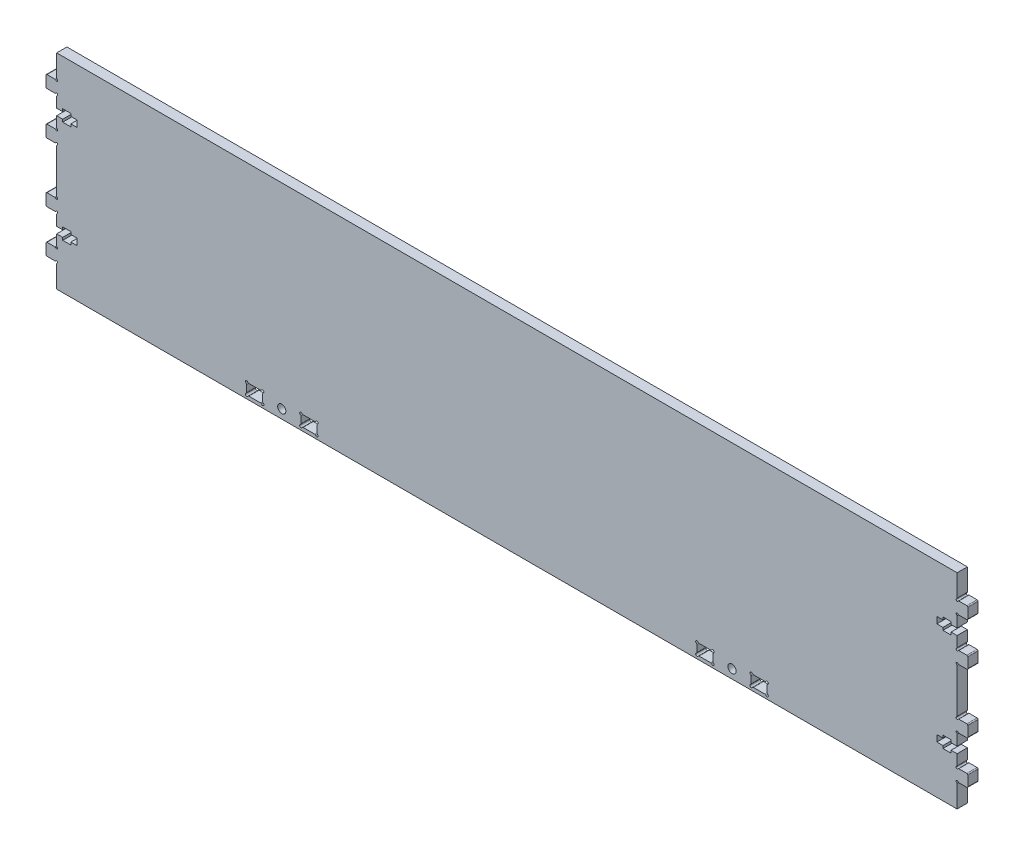
SolidWorks part; units mm, degrees
ref_plane "Alzado" through (0, 0, 0) normal (0, 0, 1) x (1, 0, 0)
ref_plane "Planta" through (0, 0, 0) normal (0, 1, 0) x (1, 0, 0)
ref_plane "Vista lateral" through (0, 0, 0) normal (1, 0, 0) x (0, 0, -1)
sketch "Croquis1" plane through (0, 0, 0) normal (0, 0, 1) x (1, 0, 0)
  line L0 (-176, 0) -> (-196, 0) construction
  line L2 (-175.9989, 28.5513) -> (-175.9989, 11.4487)
  line L3 (-175.9989, -20) -> (176.0011, -20)
  line L4 (-176.6843, -10.7633) -> (-179.7689, -10.7633)
  line L7 (176.0011, 1.2663) -> (176.0011, -1.2663) construction
  line L12 (-175.9989, -11.4487) -> (-175.9989, -20)
  line L27 (-168.0847, 0) -> (168.0869, 0) construction
  line L36 (-175.9989, -18.5) -> (176.0011, -18.5) construction
  line L46 (-175.9989, -14.5) -> (176.0011, -14.5) construction
  line L47 (-180.1646, -10.3676) -> (-180.1646, -6.4105)
  line L48 (-179.7689, -6.0148) -> (-176.6843, -6.0148)
  line L49 (-175.9989, -1.2663) -> (-173.6247, -1.2663)
  line L50 (-173.6247, -1.2663) -> (-173.6247, -2.2753)
  line L51 (-173.6247, -2.2753) -> (-170.459, -2.2753)
  line L52 (-170.459, -2.2753) -> (-170.459, -1.2663)
  line L53 (-170.459, -1.2663) -> (-168.0847, -1.2663)
  line L54 (-168.0847, -1.2663) -> (-168.0847, 1.2663)
  line L55 (-168.0847, 1.2663) -> (-170.459, 1.2663)
  line L56 (-170.459, 1.2663) -> (-170.459, 2.2753)
  line L57 (-170.459, 2.2753) -> (-173.6247, 2.2753)
  line L58 (-173.6247, 2.2753) -> (-173.6247, 1.2663)
  line L59 (-173.6247, 1.2663) -> (-175.9989, 1.2663)
  line L60 (-175.9989, 1.2663) -> (-175.9989, 5.3294)
  line L61 (-176.6843, 6.0148) -> (-179.7689, 6.0148)
  line L62 (-180.1646, 6.4105) -> (-180.1646, 10.3676)
  line L63 (-179.7689, 10.7633) -> (-176.6843, 10.7633)
  line L64 (-175.9989, -1.2663) -> (-175.9989, -5.3294)
  line L65 (176.0011, -11.4487) -> (176.0011, -20)
  line L66 (176.0011, -1.2663) -> (176.0011, -5.3294)
  line L67 (179.7711, 10.7633) -> (176.6865, 10.7633)
  line L68 (180.1668, 6.4105) -> (180.1668, 10.3676)
  line L69 (176.6865, 6.0148) -> (179.7711, 6.0148)
  line L70 (176.0011, 1.2663) -> (176.0011, 5.3294)
  line L71 (173.6269, 1.2663) -> (176.0011, 1.2663)
  line L72 (173.6269, 2.2753) -> (173.6269, 1.2663)
  line L73 (170.4612, 2.2753) -> (173.6269, 2.2753)
  line L74 (170.4612, 1.2663) -> (170.4612, 2.2753)
  line L75 (168.0869, 1.2663) -> (170.4612, 1.2663)
  line L76 (168.0869, -1.2663) -> (168.0869, 1.2663)
  line L77 (170.4612, -1.2663) -> (168.0869, -1.2663)
  line L78 (170.4612, -2.2753) -> (170.4612, -1.2663)
  line L79 (173.6269, -2.2753) -> (170.4612, -2.2753)
  line L80 (173.6269, -1.2663) -> (173.6269, -2.2753)
  line L81 (176.0011, -1.2663) -> (173.6269, -1.2663)
  line L82 (179.7711, -6.0148) -> (176.6865, -6.0148)
  line L83 (180.1668, -10.3676) -> (180.1668, -6.4105)
  line L84 (176.6865, -10.7633) -> (179.7711, -10.7633)
  line L85 (96.3671, -14.35) -> (100.8351, -14.35)
  line L86 (88.0011, -34.8253) -> (88.0011, -20) construction
  line L131 (176.0011, 28.5513) -> (176.0011, 11.4487)
  line L136 (101.7011, -15.2161) -> (101.7011, -17.7839)
  line L138 (-87.9989, -34.8253) -> (-87.9989, -20) construction
  line L139 (100.8351, -18.65) -> (96.3671, -18.65)
  line L140 (95.5011, -17.7839) -> (95.5011, -15.2161)
  line L141 (75.1671, -14.35) -> (79.6351, -14.35)
  line L142 (80.5011, -15.2161) -> (80.5011, -17.7839)
  line L143 (79.6351, -18.65) -> (75.1671, -18.65)
  line L144 (74.3011, -17.7839) -> (74.3011, -15.2161)
  line L145 (-87.9989, -18.5) -> (-87.9989, -14.5) construction
  line L146 (-101.6989, -17.7839) -> (-101.6989, -15.2161)
  line L147 (-74.2989, -15.2161) -> (-74.2989, -17.7839)
  line L148 (-95.4989, -15.2161) -> (-95.4989, -17.7839)
  line L149 (-96.3649, -18.65) -> (-100.8329, -18.65)
  line L150 (-100.8329, -14.35) -> (-96.3649, -14.35)
  line L151 (-79.6329, -14.35) -> (-75.1649, -14.35)
  line L152 (-80.4989, -17.7839) -> (-80.4989, -15.2161)
  line L153 (-75.1649, -18.65) -> (-79.6329, -18.65)
  line L154 (88.0011, -18.5) -> (88.0011, -14.5) construction
  line L161 (-168.0847, 40) -> (168.0869, 40) construction
  line L162 (176.0011, 38.7337) -> (176.0011, 41.2663) construction
  line L163 (-176, 40) -> (-196, 40) construction
  line L180 (176.6865, 50.7633) -> (179.7711, 50.7633)
  line L181 (180.1668, 50.3676) -> (180.1668, 46.4105)
  line L182 (179.7711, 46.0148) -> (176.6865, 46.0148)
  line L183 (176.0011, 41.2663) -> (173.6269, 41.2663)
  line L184 (173.6269, 41.2663) -> (173.6269, 42.2753)
  line L185 (173.6269, 42.2753) -> (170.4612, 42.2753)
  line L186 (170.4612, 42.2753) -> (170.4612, 41.2663)
  line L187 (170.4612, 41.2663) -> (168.0869, 41.2663)
  line L188 (168.0869, 41.2663) -> (168.0869, 38.7337)
  line L189 (168.0869, 38.7337) -> (170.4612, 38.7337)
  line L190 (170.4612, 38.7337) -> (170.4612, 37.7247)
  line L191 (170.4612, 37.7247) -> (173.6269, 37.7247)
  line L192 (173.6269, 37.7247) -> (173.6269, 38.7337)
  line L193 (173.6269, 38.7337) -> (176.0011, 38.7337)
  line L194 (176.0011, 38.7337) -> (176.0011, 34.6706)
  line L195 (176.6865, 33.9852) -> (179.7711, 33.9852)
  line L196 (180.1668, 33.5895) -> (180.1668, 29.6324)
  line L197 (179.7711, 29.2367) -> (176.6865, 29.2367)
  line L198 (176.0011, 41.2663) -> (176.0011, 45.3294)
  line L199 (176.0011, 51.4487) -> (176.0011, 60)
  line L200 (-175.9989, 41.2663) -> (-175.9989, 45.3294)
  line L201 (-179.7689, 29.2367) -> (-176.6843, 29.2367)
  line L202 (-180.1646, 33.5895) -> (-180.1646, 29.6324)
  line L203 (-176.6843, 33.9852) -> (-179.7689, 33.9852)
  line L204 (-175.9989, 38.7337) -> (-175.9989, 34.6706)
  line L205 (-173.6247, 38.7337) -> (-175.9989, 38.7337)
  line L206 (-173.6247, 37.7247) -> (-173.6247, 38.7337)
  line L207 (-170.459, 37.7247) -> (-173.6247, 37.7247)
  line L208 (-170.459, 38.7337) -> (-170.459, 37.7247)
  line L209 (-168.0847, 38.7337) -> (-170.459, 38.7337)
  line L210 (-168.0847, 41.2663) -> (-168.0847, 38.7337)
  line L211 (-170.459, 41.2663) -> (-168.0847, 41.2663)
  line L212 (-170.459, 42.2753) -> (-170.459, 41.2663)
  line L213 (-173.6247, 42.2753) -> (-170.459, 42.2753)
  line L214 (-173.6247, 41.2663) -> (-173.6247, 42.2753)
  line L215 (-175.9989, 41.2663) -> (-173.6247, 41.2663)
  line L216 (-179.7689, 46.0148) -> (-176.6843, 46.0148)
  line L217 (-180.1646, 50.3676) -> (-180.1646, 46.4105)
  line L218 (-175.9989, 51.4487) -> (-175.9989, 60)
  line L219 (-176.6843, 50.7633) -> (-179.7689, 50.7633)
  line L220 (-175.9989, 60) -> (176.0011, 60)
  arc A32 (-175.801, -11.106) -> (-175.9989, -11.4487) centre (-175.6032, -11.4487) ccw
  arc A33 (-175.801, -11.106) -> (-176.3416, -10.5654) centre (-175.9989, -10.7633) ccw
  arc A34 (-176.6843, -10.7633) -> (-176.3416, -10.5654) centre (-176.6843, -10.3676) ccw
  arc A35 (-180.1646, -10.3676) -> (-179.7689, -10.7633) centre (-179.7689, -10.3676) ccw
  arc A36 (-179.7689, -6.0148) -> (-180.1646, -6.4105) centre (-179.7689, -6.4105) ccw
  arc A37 (-176.3416, -6.2126) -> (-176.6843, -6.0148) centre (-176.6843, -6.4105) ccw
  arc A38 (-176.3416, -6.2126) -> (-175.801, -5.6721) centre (-175.9989, -6.0148) ccw
  arc A39 (-175.9989, -5.3294) -> (-175.801, -5.6721) centre (-175.6032, -5.3294) ccw
  arc A40 (-175.801, 5.6721) -> (-175.9989, 5.3294) centre (-175.6032, 5.3294) ccw
  arc A41 (-175.801, 5.6721) -> (-176.3416, 6.2126) centre (-175.9989, 6.0148) ccw
  arc A42 (-176.6843, 6.0148) -> (-176.3416, 6.2126) centre (-176.6843, 6.4105) ccw
  arc A43 (-180.1646, 6.4105) -> (-179.7689, 6.0148) centre (-179.7689, 6.4105) ccw
  arc A44 (-179.7689, 10.7633) -> (-180.1646, 10.3676) centre (-179.7689, 10.3676) ccw
  arc A45 (-176.3416, 10.5654) -> (-176.6843, 10.7633) centre (-176.6843, 10.3676) ccw
  arc A46 (-176.3416, 10.5654) -> (-175.801, 11.106) centre (-175.9989, 10.7633) ccw
  arc A47 (-175.9989, 11.4487) -> (-175.801, 11.106) centre (-175.6032, 11.4487) ccw
  arc A48 (176.0011, 11.4487) -> (175.8033, 11.106) centre (175.6054, 11.4487) cw
  arc A49 (176.3438, 10.5654) -> (175.8033, 11.106) centre (176.0011, 10.7633) cw
  arc A50 (176.3438, 10.5654) -> (176.6865, 10.7633) centre (176.6865, 10.3676) cw
  arc A51 (179.7711, 10.7633) -> (180.1668, 10.3676) centre (179.7711, 10.3676) cw
  arc A52 (180.1668, 6.4105) -> (179.7711, 6.0148) centre (179.7711, 6.4105) cw
  arc A53 (176.6865, 6.0148) -> (176.3438, 6.2126) centre (176.6865, 6.4105) cw
  arc A54 (175.8033, 5.6721) -> (176.3438, 6.2126) centre (176.0011, 6.0148) cw
  arc A55 (175.8033, 5.6721) -> (176.0011, 5.3294) centre (175.6054, 5.3294) cw
  arc A56 (176.0011, -5.3294) -> (175.8033, -5.6721) centre (175.6054, -5.3294) cw
  arc A57 (176.3438, -6.2126) -> (175.8033, -5.6721) centre (176.0011, -6.0148) cw
  arc A58 (176.3438, -6.2126) -> (176.6865, -6.0148) centre (176.6865, -6.4105) cw
  arc A59 (179.7711, -6.0148) -> (180.1668, -6.4105) centre (179.7711, -6.4105) cw
  arc A60 (180.1668, -10.3676) -> (179.7711, -10.7633) centre (179.7711, -10.3676) cw
  arc A61 (176.6865, -10.7633) -> (176.3438, -10.5654) centre (176.6865, -10.3676) cw
  arc A62 (175.8033, -11.106) -> (176.3438, -10.5654) centre (176.0011, -10.7633) cw
  arc A63 (175.8033, -11.106) -> (176.0011, -11.4487) centre (175.6054, -11.4487) cw
  arc A96 (95.5011, -15.2161) -> (95.2511, -14.7831) centre (95.0011, -15.2161) ccw
  arc A97 (95.9341, -14.1) -> (95.2511, -14.7831) centre (95.5011, -14.35) ccw
  arc A98 (95.9341, -14.1) -> (96.3671, -14.35) centre (96.3671, -13.85) ccw
  arc A99 (100.8351, -14.35) -> (101.2681, -14.1) centre (100.8351, -13.85) ccw
  arc A100 (101.9511, -14.783) -> (101.2681, -14.1) centre (101.7011, -14.35) ccw
  arc A101 (101.9511, -14.783) -> (101.7011, -15.2161) centre (102.2011, -15.2161) ccw
  arc A102 (101.7011, -17.7839) -> (101.9511, -18.2169) centre (102.2011, -17.7839) ccw
  arc A103 (101.2681, -18.9) -> (101.9511, -18.2169) centre (101.7011, -18.65) ccw
  arc A104 (101.2681, -18.9) -> (100.8351, -18.65) centre (100.8351, -19.15) ccw
  arc A105 (96.3671, -18.65) -> (95.9341, -18.9) centre (96.3671, -19.15) ccw
  arc A106 (95.2511, -18.2169) -> (95.9341, -18.9) centre (95.5011, -18.65) ccw
  arc A107 (95.2511, -18.2169) -> (95.5011, -17.7839) centre (95.0011, -17.7839) ccw
  arc A108 (74.3011, -15.2161) -> (74.0511, -14.7831) centre (73.8011, -15.2161) ccw
  arc A109 (74.7341, -14.1) -> (74.0511, -14.7831) centre (74.3011, -14.35) ccw
  arc A110 (74.7341, -14.1) -> (75.1671, -14.35) centre (75.1671, -13.85) ccw
  arc A111 (79.6351, -14.35) -> (80.0681, -14.1) centre (79.6351, -13.85) ccw
  arc A112 (80.7511, -14.783) -> (80.0681, -14.1) centre (80.5011, -14.35) ccw
  arc A113 (80.7511, -14.783) -> (80.5011, -15.2161) centre (81.0011, -15.2161) ccw
  arc A114 (80.5011, -17.7839) -> (80.7511, -18.2169) centre (81.0011, -17.7839) ccw
  arc A115 (80.0681, -18.9) -> (80.7511, -18.2169) centre (80.5011, -18.65) ccw
  arc A116 (80.0681, -18.9) -> (79.6351, -18.65) centre (79.6351, -19.15) ccw
  arc A117 (75.1671, -18.65) -> (74.7341, -18.9) centre (75.1671, -19.15) ccw
  arc A118 (74.0511, -18.217) -> (74.7341, -18.9) centre (74.3011, -18.65) ccw
  arc A119 (74.0511, -18.217) -> (74.3011, -17.7839) centre (73.8011, -17.7839) ccw
  circle A120 centre (88.0011, -16.5) radius 1.6
  arc A121 (-101.6989, -15.2161) -> (-101.9489, -14.7831) centre (-102.1989, -15.2161) ccw
  arc A122 (-79.6329, -18.65) -> (-80.0659, -18.9) centre (-79.6329, -19.15) ccw
  arc A123 (-74.0489, -14.783) -> (-74.2989, -15.2161) centre (-73.7989, -15.2161) ccw
  arc A124 (-96.3649, -14.35) -> (-95.9319, -14.1) centre (-96.3649, -13.85) ccw
  arc A125 (-95.2489, -14.783) -> (-95.9319, -14.1) centre (-95.4989, -14.35) ccw
  arc A126 (-95.9319, -18.9) -> (-95.2489, -18.2169) centre (-95.4989, -18.65) ccw
  arc A127 (-80.7489, -18.2169) -> (-80.4989, -17.7839) centre (-80.9989, -17.7839) ccw
  circle A128 centre (-87.9989, -16.5) radius 1.6
  arc A129 (-74.2989, -17.7839) -> (-74.0489, -18.2169) centre (-73.7989, -17.7839) ccw
  arc A130 (-101.2659, -14.1) -> (-101.9489, -14.7831) centre (-101.6989, -14.35) ccw
  arc A131 (-80.0659, -14.1) -> (-79.6329, -14.35) centre (-79.6329, -13.85) ccw
  arc A132 (-95.2489, -14.783) -> (-95.4989, -15.2161) centre (-94.9989, -15.2161) ccw
  arc A133 (-80.0659, -14.1) -> (-80.7489, -14.7831) centre (-80.4989, -14.35) ccw
  arc A134 (-101.9489, -18.217) -> (-101.6989, -17.7839) centre (-102.1989, -17.7839) ccw
  arc A135 (-101.2659, -14.1) -> (-100.8329, -14.35) centre (-100.8329, -13.85) ccw
  arc A136 (-80.7489, -18.2169) -> (-80.0659, -18.9) centre (-80.4989, -18.65) ccw
  arc A137 (-95.9319, -18.9) -> (-96.3649, -18.65) centre (-96.3649, -19.15) ccw
  arc A138 (-80.4989, -15.2161) -> (-80.7489, -14.7831) centre (-80.9989, -15.2161) ccw
  arc A139 (-100.8329, -18.65) -> (-101.2659, -18.9) centre (-100.8329, -19.15) ccw
  arc A140 (-75.1649, -14.35) -> (-74.7319, -14.1) centre (-75.1649, -13.85) ccw
  arc A141 (-74.0489, -14.783) -> (-74.7319, -14.1) centre (-74.2989, -14.35) ccw
  arc A142 (-74.7319, -18.9) -> (-74.0489, -18.2169) centre (-74.2989, -18.65) ccw
  arc A143 (-74.7319, -18.9) -> (-75.1649, -18.65) centre (-75.1649, -19.15) ccw
  arc A144 (-95.4989, -17.7839) -> (-95.2489, -18.2169) centre (-94.9989, -17.7839) ccw
  arc A145 (-101.9489, -18.217) -> (-101.2659, -18.9) centre (-101.6989, -18.65) ccw
  circle A146 centre (-87.9989, -16.5) radius 2.8 construction
  circle A147 centre (88.0011, -16.5) radius 2.8 construction
  arc A200 (175.8033, 51.106) -> (176.0011, 51.4487) centre (175.6054, 51.4487) ccw
  arc A201 (175.8033, 51.106) -> (176.3438, 50.5654) centre (176.0011, 50.7633) ccw
  arc A202 (176.6865, 50.7633) -> (176.3438, 50.5654) centre (176.6865, 50.3676) ccw
  arc A203 (180.1668, 50.3676) -> (179.7711, 50.7633) centre (179.7711, 50.3676) ccw
  arc A204 (179.7711, 46.0148) -> (180.1668, 46.4105) centre (179.7711, 46.4105) ccw
  arc A205 (176.3438, 46.2126) -> (176.6865, 46.0148) centre (176.6865, 46.4105) ccw
  arc A206 (176.3438, 46.2126) -> (175.8033, 45.6721) centre (176.0011, 46.0148) ccw
  arc A207 (176.0011, 45.3294) -> (175.8033, 45.6721) centre (175.6054, 45.3294) ccw
  arc A208 (175.8033, 34.3279) -> (176.0011, 34.6706) centre (175.6054, 34.6706) ccw
  arc A209 (175.8033, 34.3279) -> (176.3438, 33.7874) centre (176.0011, 33.9852) ccw
  arc A210 (176.6865, 33.9852) -> (176.3438, 33.7874) centre (176.6865, 33.5895) ccw
  arc A211 (180.1668, 33.5895) -> (179.7711, 33.9852) centre (179.7711, 33.5895) ccw
  arc A212 (179.7711, 29.2367) -> (180.1668, 29.6324) centre (179.7711, 29.6324) ccw
  arc A213 (176.3438, 29.4346) -> (176.6865, 29.2367) centre (176.6865, 29.6324) ccw
  arc A214 (176.3438, 29.4346) -> (175.8033, 28.894) centre (176.0011, 29.2367) ccw
  arc A215 (176.0011, 28.5513) -> (175.8033, 28.894) centre (175.6054, 28.5513) ccw
  arc A216 (-175.9989, 28.5513) -> (-175.801, 28.894) centre (-175.6032, 28.5513) cw
  arc A217 (-176.3416, 29.4346) -> (-175.801, 28.894) centre (-175.9989, 29.2367) cw
  arc A218 (-176.3416, 29.4346) -> (-176.6843, 29.2367) centre (-176.6843, 29.6324) cw
  arc A219 (-179.7689, 29.2367) -> (-180.1646, 29.6324) centre (-179.7689, 29.6324) cw
  arc A220 (-180.1646, 33.5895) -> (-179.7689, 33.9852) centre (-179.7689, 33.5895) cw
  arc A221 (-176.6843, 33.9852) -> (-176.3416, 33.7874) centre (-176.6843, 33.5895) cw
  arc A222 (-175.801, 34.3279) -> (-176.3416, 33.7874) centre (-175.9989, 33.9852) cw
  arc A223 (-175.801, 34.3279) -> (-175.9989, 34.6706) centre (-175.6032, 34.6706) cw
  arc A224 (-175.9989, 45.3294) -> (-175.801, 45.6721) centre (-175.6032, 45.3294) cw
  arc A225 (-176.3416, 46.2126) -> (-175.801, 45.6721) centre (-175.9989, 46.0148) cw
  arc A226 (-176.3416, 46.2126) -> (-176.6843, 46.0148) centre (-176.6843, 46.4105) cw
  arc A227 (-179.7689, 46.0148) -> (-180.1646, 46.4105) centre (-179.7689, 46.4105) cw
  arc A228 (-180.1646, 50.3676) -> (-179.7689, 50.7633) centre (-179.7689, 50.3676) cw
  arc A229 (-176.6843, 50.7633) -> (-176.3416, 50.5654) centre (-176.6843, 50.3676) cw
  arc A230 (-175.801, 51.106) -> (-176.3416, 50.5654) centre (-175.9989, 50.7633) cw
  arc A231 (-175.801, 51.106) -> (-175.9989, 51.4487) centre (-175.6032, 51.4487) cw
  point P0 (0, 0)
  point P470 (0, 40)
  dimension "D3" = 4
  dimension "D2" = 1.5
extrude "Saliente-Extruir1" add sketch "Croquis1" along normal blind 4
